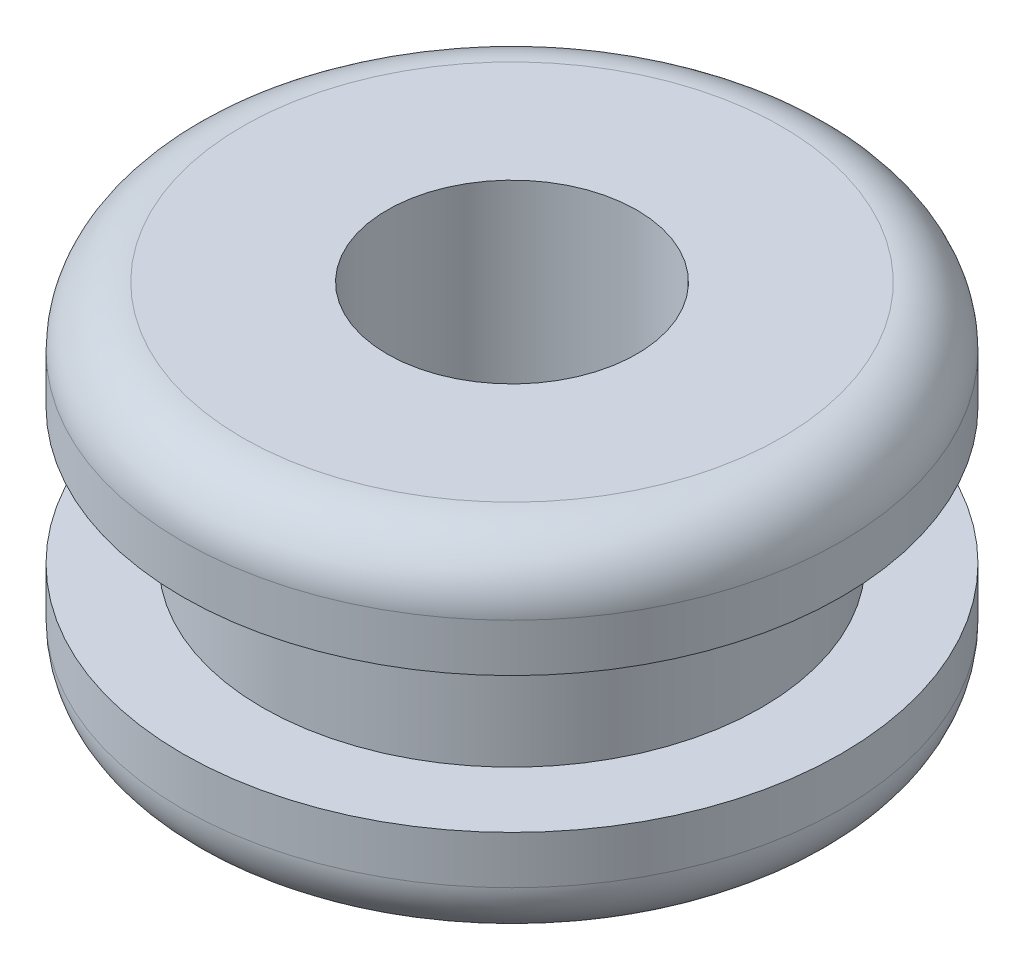
SolidWorks part; units mm, degrees
ref_plane "Front Plane" through (0, 0, 0) normal (0, 0, 1) x (1, 0, 0)
ref_plane "Top Plane" through (0, 0, 0) normal (0, 1, 0) x (1, 0, 0)
ref_plane "Right Plane" through (0, 0, 0) normal (1, 0, 0) x (0, 0, -1)
sketch "Sketch1" plane through (0, 0, 0) normal (0, 1, 0) x (1, 0, 0)
  circle A0 centre (0, 0) radius 4.191
  dimension "D1" = 8.382
extrude "Boss-Extrude1" add sketch "Sketch1" along normal blind 1.3716
sketch "Sketch2" plane through (0, 1.3716, 0) normal (0, 1, 0) x (1, 0, 0)
  circle A0 centre (0, 0) radius 3.175
  dimension "D1" = 6.35
extrude "Boss-Extrude2" add sketch "Sketch2" along normal blind 1.7272
sketch "Sketch3" plane through (0, 3.0988, 0) normal (0, 1, 0) x (1, 0, 0)
  circle A0 centre (0, 0) radius 4.191
  dimension "D1" = 8.382
extrude "Boss-Extrude3" add sketch "Sketch3" along normal blind 1.3716
sketch "Sketch4" plane through (0, 4.4704, 0) normal (0, 1, 0) x (1, 0, 0)
  circle A0 centre (0, 0) radius 1.5875
  dimension "D1" = 3.175
extrude "Cut-Extrude1" cut sketch "Sketch4" against normal through all
fillet "Fillet1" radius 0.762 2 edges at (0, 4.4704, 4.191) (0, 0, 4.191)
